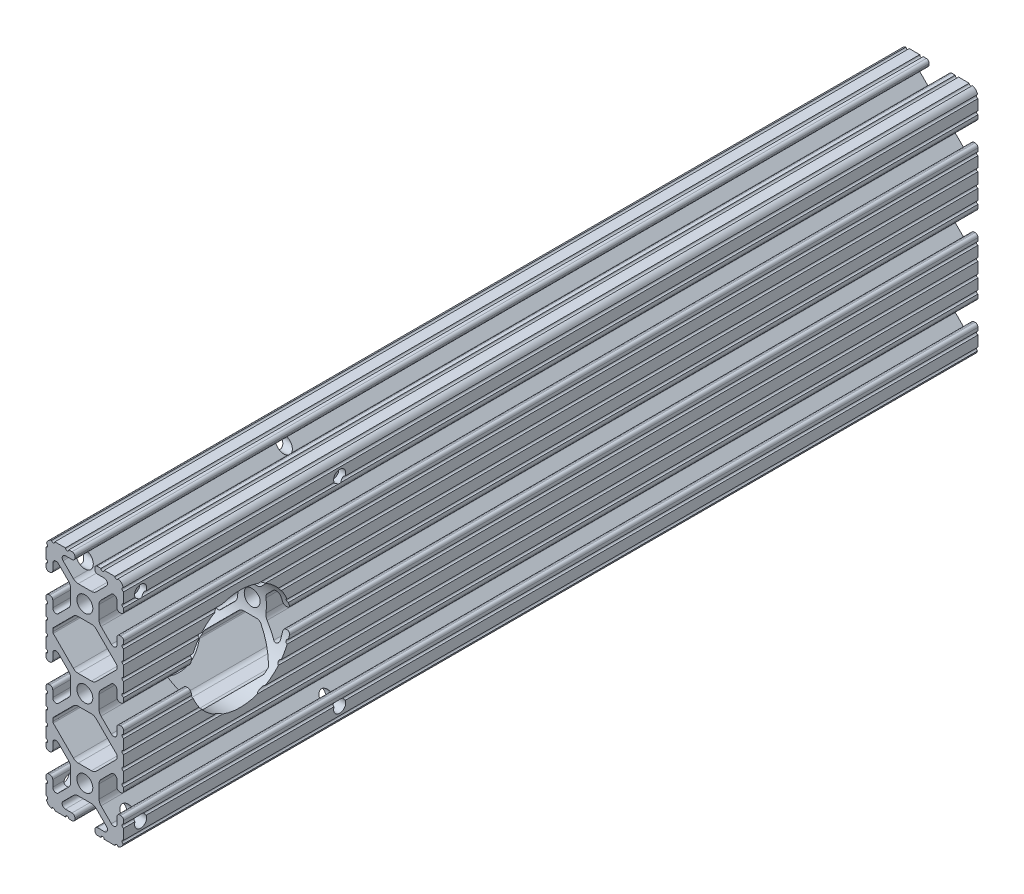
SolidWorks part; units mm, degrees
material "6061-T6 (SS)"
ref_plane "Front Plane" through (0, 0, 0) normal (0, 0, 1) x (1, 0, 0)
ref_plane "Top Plane" through (0, 0, 0) normal (0, 1, 0) x (1, 0, 0)
ref_plane "Right Plane" through (0, 0, 0) normal (1, 0, 0) x (0, 0, -1)
sketch "Sketch2" plane through (0, 0, 0) normal (0, 0, 1) x (1, 0, 0)
  line L0 (0, 38.1) -> (0, -38.1) construction
  line L1 (-12.7, 0) -> (12.7, 0) construction
  line L2 (3.2512, -38.1) -> (12.7, -38.1)
  line L3 (12.7, -38.1) -> (12.7, -28.6512)
  line L4 (3.2512, -38.1) -> (3.2512, -35.8902)
  line L5 (3.2512, -35.8902) -> (8.9276, -35.8902)
  line L6 (8.9276, -35.8902) -> (3.0856, -30.0482)
  line L7 (0, -25.4) -> (12.7, -38.1) construction
  line L8 (12.7, -28.6512) -> (10.4902, -28.6512)
  line L9 (10.4902, -28.6512) -> (10.4902, -34.3276)
  line L10 (10.4902, -34.3276) -> (4.6482, -28.4856)
  circle A0 centre (0, -25.4) radius 2.6035
  arc A1 (6.3485, -35.8902) -> (7.1039, -34.0665) centre (6.3485, -34.8219) ccw construction
  point P8 (0, -30.0482)
  dimension "Center Hole Diameter" = 5.207
  dimension "Rail Height" = 76.2
  dimension "Rail Width" = 25.4
  dimension "T-Slot Width" = 6.5024
  dimension "Slot Inner Width" = 14.8336
  dimension "Thickness" = 2.2098
  dimension "Slot Depth" = 5.842
  dimension "D1" = 2.2098
  dimension "D2" = 50.8
sketch "Sketch3" plane through (0, 0, 0) normal (1, 0, 0) x (0, 0, -1)
  line L0 (-152.4, -38.1) -> (152.4, -38.1) construction
  line L1 (-127, 0) -> (127, 0) construction
  dimension "D1" = 25.4
  dimension "Length" = 304.8
sketch "Sketch4" plane through (0, 0, 0) normal (0, 0, 1) x (1, 0, 0)
  line L0 (4.1904, -38.1) -> (10.1173, -38.1)
  line L1 (3.2512, -38.1) -> (12.7, -38.1) construction
  line L2 (3.2512, -38.1) -> (3.2512, -35.8902) construction
  line L3 (3.2512, -35.8902) -> (8.9276, -35.8902) construction
  line L4 (3.2512, -36.8294) -> (3.2512, -37.1608)
  line L5 (4.1904, -35.8902) -> (6.3485, -35.8902)
  line L6 (0, -30.0482) -> (2.164, -30.0482)
  line L7 (8.9276, -35.8902) -> (3.0856, -30.0482) construction
  line L8 (3.7373, -30.6999) -> (7.1039, -34.0665)
  line L9 (12.7, -38.1) -> (12.7, -28.6512) construction
  line L10 (10.4902, -34.3276) -> (4.6482, -28.4856) construction
  line L11 (10.4902, -28.6512) -> (10.4902, -34.3276) construction
  line L12 (10.4902, -31.7485) -> (10.4902, -29.5904)
  line L13 (12.7, -28.6512) -> (10.4902, -28.6512) construction
  line L14 (11.4294, -28.6512) -> (11.7608, -28.6512)
  line L15 (12.7, -29.5904) -> (12.7, -35.5173)
  line L16 (8.6665, -32.5039) -> (5.2999, -29.1373)
  line L17 (4.6482, -25.4) -> (4.6482, -27.564)
  line L19 (0, -30.0482) -> (0, -28.0035)
  line L20 (0, 38.1) -> (0, -38.1) construction
  line L21 (4.6482, -25.4) -> (2.6035, -25.4)
  arc A0 (3.2512, -37.1608) -> (4.1904, -38.1) centre (4.1904, -37.1608) ccw
  circle A1 centre (0, -25.4) radius 2.6035 construction
  arc A2 (3.2512, -36.8294) -> (4.1904, -35.8902) centre (4.1904, -36.8294) cw
  arc A3 (6.3485, -35.8902) -> (7.1039, -34.0665) centre (6.3485, -34.8219) ccw
  arc A4 (2.164, -30.0482) -> (3.7373, -30.6999) centre (2.164, -32.2732) cw
  arc A5 (10.1173, -38.1) -> (12.7, -35.5173) centre (10.1173, -35.5173) ccw
  arc A6 (8.6665, -32.5039) -> (10.4902, -31.7485) centre (9.4219, -31.7485) ccw
  arc A7 (10.4902, -29.5904) -> (11.4294, -28.6512) centre (11.4294, -29.5904) cw
  arc A8 (11.7608, -28.6512) -> (12.7, -29.5904) centre (11.7608, -29.5904) cw
  arc A9 (5.2999, -29.1373) -> (4.6482, -27.564) centre (6.8732, -27.564) cw
  arc A11 (0, -28.0035) -> (2.6035, -25.4) centre (0, -25.4) ccw
  dimension "D1" = 2.5827
  dimension "D2" = 2.225
  dimension "D3" = 0.9392
extrude "Boss-Extrude1" add sketch "Sketch4" along normal mid plane 279.4
sketch "Sketch5" plane through (0, 0, 0) normal (0, 0, 1) x (1, 0, 0)
  line L0 (3.2512, -38.1) -> (12.7, -38.1) construction
  line L1 (4.1904, -35.8902) -> (6.3485, -35.8902) construction
  line L3 (0, -25.4) -> (12.7, -38.1) construction
  line L4 (6.3485, -35.8902) -> (6.3485, -38.1) construction
  line L5 (8.9276, -35.8902) -> (3.0856, -30.0482) construction
  circle A0 centre (10.3562, -38.1) radius 0.5524
  circle A1 centre (5.796, -38.1) radius 0.5524
  circle A2 centre (12.7, -35.7562) radius 0.5525
  circle A3 centre (12.7, -31.196) radius 0.5525
  point P10 (5.2694, -35.8902)
  point P12 (9.4219, -31.7485)
  dimension "D1" = 1.1049
extrude "Cut-Extrude1" cut sketch "Sketch5" against normal through all both and the other way through all
mirror "Mirror1" about plane through (4.6482, -25.4, 139.7) normal (0, -1, 0) of bodies 137 134
sketch "Sketch6" plane through (0, 0, 0) normal (0, 0, 1) x (1, 0, 0)
  line L0 (12.7, -14.4914) -> (12.7, -12.7)
  line L1 (12.7, -12.7) -> (9.8037, -12.7)
  line L3 (9.8037, -12.7) -> (9.8037, -15.5963)
  line L4 (9.8037, -15.5963) -> (12.7, -15.5963)
  line L5 (6.3485, -12.7) -> (9.8037, -12.7) construction
  circle A0 centre (12.7, -15.0438) radius 0.5525 construction
  arc A1 (12.7, -14.4914) -> (12.7, -15.5963) centre (12.7, -15.0438) ccw
  arc A4 (9.8037, -12.7) -> (10.8954, -12.82) centre (10.3562, -12.7) ccw construction
extrude "Boss-Extrude2" add sketch "Sketch6" along normal mid plane 279.4
sketch "Sketch7" plane through (0, 0, 0) normal (0, 0, 1) x (1, 0, 0)
  line L0 (5.4206, -18.4168) -> (10.3284, -13.509)
  line L1 (3.7373, -20.1001) -> (7.1039, -16.7335) construction
  line L2 (10.4902, -13.1184) -> (10.4902, -12.7)
  line L3 (0, -12.7) -> (10.4902, -12.7)
  line L5 (0, -12.7) -> (5.4206, -18.4168)
  line L7 (0, 38.1) -> (0, -38.1) construction
  line L8 (6.3485, -12.7) -> (12.7, -12.7) construction
  arc A0 (10.3284, -13.509) -> (10.4902, -13.1184) centre (9.9377, -13.1184) ccw
  circle A3 centre (12.7, -15.0438) radius 0.5525 construction
extrude "Cut-Extrude2" cut sketch "Sketch7" against normal through all both and the other way through all
mirror "Mirror2" about plane through (4.1904, -12.7, 139.7) normal (0, -1, 0) of bodies 139 135
other "SurfaceCut1"
mirror "Mirror3" about plane through (0, 0, 0) normal (1, 0, 0) of bodies 142 136
mirror "Mirror4" about plane through (0, 0, 0) normal (0, 1, 0) of bodies 140
sketch "Sketch8" plane through (-12.7, 0, 0) normal (-1, 0, 0) x (0, 0, 1)
  line L0 (139.7, 0) -> (101.6, 0) construction
  line L1 (139.7, 2.164) -> (139.7, -2.164) construction
  line L2 (134.1501, 32.5501) -> (139.7, 32.5501) construction
  line L3 (69.0499, -32.5501) -> (134.1501, -32.5501) construction
  line L4 (69.0499, -32.5501) -> (69.0499, 32.5501) construction
  line L5 (69.0499, 32.5501) -> (134.1501, 32.5501) construction
  line L6 (134.1501, -32.5501) -> (134.1501, 32.5501) construction
  line L7 (69.0499, -32.5501) -> (134.1501, 32.5501) construction
  line L8 (69.0499, 32.5501) -> (134.1501, -32.5501) construction
  line L9 (134.1501, 32.5501) -> (134.1501, 38.1) construction
  line L10 (139.7, 35.2037) -> (139.7, 31.7485) construction
  line L11 (-139.7, 38.1) -> (139.7, 38.1) construction
  circle A0 centre (134.1501, 32.5501) radius 1.9812
  circle A1 centre (69.0499, 32.5501) radius 1.9812
  circle A2 centre (69.0499, -32.5501) radius 1.9812
  circle A3 centre (134.1501, -32.5501) radius 1.9812
  circle A4 centre (101.6, 0) radius 16.637
  point P6 (101.6, 0)
  dimension "D1" = 3.9624
  dimension "D3" = 33.274
  dimension "D2" = 65.1002
extrude "Cut-Extrude3" cut sketch "Sketch8" against normal through all
equation "\"D1@Boss-Extrude1\" = \"azimuth_vertictal_rail_length_long\""
equation "\"D1@Sketch2\"=\"Thickness@Sketch2\""
equation "\"D2@Sketch4\"=\"Slot Inner Width@Sketch2\"*0.15"
equation "\"D1@Sketch4\"=\"D3@Sketch4\"*2.75"
equation "\"D3@Sketch4\"=\"Thickness@Sketch2\"*0.425"
equation "\"D1@Sketch5\"= \"Thickness@Sketch2\" * 0.5"
equation "\"D1@Boss-Extrude2\"= \"azimuth_vertictal_rail_length_long\""
equation "\"azimuth_horizontal_rail_length\"=(\"altitude_horizontal_rail_length\"+6in-0.29in)"
equation "\"wall_screw_clearance_diameter\"=4.3mm"
equation "\"azimuth_vertictal_rail_length_short\"=(\"altitude_vertictal_rail_length\"-5in)"
equation "\"azimuth_vertictal_rail_length_long\"=(\"azimuth_vertictal_rail_length_short\"+4in)"
equation "\"altitude_horizontal_rail_length\"=10in"
equation "\"altitude_vertictal_rail_length\"=12in"
